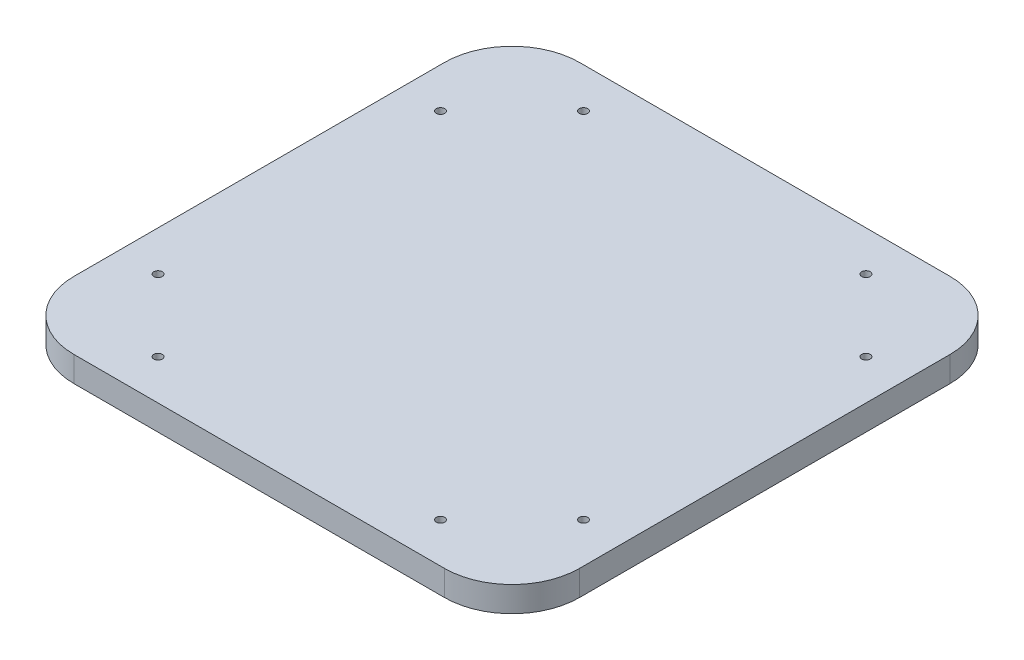
SolidWorks part; units mm, degrees
ref_plane "Front Plane" through (0, 0, 0) normal (0, 0, 1) x (1, 0, 0)
ref_plane "Top Plane" through (0, 0, 0) normal (0, 1, 0) x (1, 0, 0)
ref_plane "Right Plane" through (0, 0, 0) normal (1, 0, 0) x (0, 0, -1)
sketch "Sketch1" plane through (0, 0, 0) normal (0, 1, 0) x (1, 0, 0)
  line L1 (-150, -150) -> (150, -150)
  line L2 (-150, -150) -> (-150, 150)
  line L3 (-150, 150) -> (150, 150)
  line L4 (150, -150) -> (150, 150)
  line L5 (-150, -150) -> (150, 150) construction
  line L6 (-150, 150) -> (150, -150) construction
  point P0 (0, 0)
  dimension "D1" = 300
  dimension "D2" = 300
extrude "Boss-Extrude1" add sketch "Sketch1" along normal blind 15
sketch "Sketch2" plane through (0, 15, 0) normal (0, 1, 0) x (1, 0, 0)
  line L0 (-126.2132, 83.7868) -> (-83.7868, 126.2132) construction
  line L1 (-105, -105) -> (105, -105) construction
  line L2 (-105, -105) -> (-105, 105) construction
  line L3 (-105, 105) -> (105, 105) construction
  line L4 (105, -105) -> (105, 105) construction
  line L5 (-105, -105) -> (105, 105) construction
  line L6 (-105, 105) -> (105, -105) construction
  line L7 (-130.725, 85.9416) -> (-118.5355, 111.4645) construction
  line L8 (-111.4645, 118.5355) -> (-85.9416, 130.725) construction
  line L9 (-124.0584, 79.275) -> (-98.5355, 91.4645) construction
  line L10 (-91.4645, 98.5355) -> (-79.275, 124.0584) construction
  line L11 (83.7868, 126.2132) -> (126.2132, 83.7868) construction
  line L12 (79.275, 124.0584) -> (91.4645, 98.5355) construction
  line L13 (85.9416, 130.725) -> (111.4645, 118.5355) construction
  line L14 (118.5355, 111.4645) -> (130.725, 85.9416) construction
  line L15 (98.5355, 91.4645) -> (124.0584, 79.275) construction
  line L16 (126.2132, -83.7868) -> (83.7868, -126.2132) construction
  line L17 (124.0584, -79.275) -> (98.5355, -91.4645) construction
  line L18 (130.725, -85.9416) -> (118.5355, -111.4645) construction
  line L19 (111.4645, -118.5355) -> (85.9416, -130.725) construction
  line L20 (91.4645, -98.5355) -> (79.275, -124.0584) construction
  line L21 (-83.7868, -126.2132) -> (-126.2132, -83.7868) construction
  line L22 (-79.275, -124.0584) -> (-91.4645, -98.5355) construction
  line L23 (-85.9416, -130.725) -> (-111.4645, -118.5355) construction
  line L24 (-118.5355, -111.4645) -> (-130.725, -85.9416) construction
  line L25 (-98.5355, -91.4645) -> (-124.0584, -79.275) construction
  circle A0 centre (-105, 105) radius 5 construction
  circle A1 centre (-105, 105) radius 15 construction
  circle A2 centre (-83.7868, 126.2132) radius 5 construction
  circle A3 centre (-126.2132, 83.7868) radius 5 construction
  circle A4 centre (105, 105) radius 15 construction
  circle A5 centre (83.7868, 126.2132) radius 5 construction
  circle A6 centre (126.2132, 83.7868) radius 5 construction
  circle A7 centre (105, -105) radius 15 construction
  circle A8 centre (126.2132, -83.7868) radius 5 construction
  circle A9 centre (83.7868, -126.2132) radius 5 construction
  circle A10 centre (-105, -105) radius 15 construction
  circle A11 centre (-83.7868, -126.2132) radius 5 construction
  circle A12 centre (-126.2132, -83.7868) radius 5 construction
  point P0 (0, 0)
  point P11 (-105, 105)
  point P66 (0, 0)
  dimension "D2" = 30
  dimension "D3" = 10
  dimension "D4" = 10
  dimension "D5" = 10
  dimension "D1" = 210
  dimension "D6" = 60
  dimension "D7" = 45
  dimension "D8" = 4
sketch "Sketch3" plane through (0, 15, 0) normal (0, 1, 0) x (1, 0, 0)
  circle A0 centre (-83.7868, 126.2132) radius 2.5
  circle A1 centre (-126.2132, 83.7868) radius 2.5
  circle A2 centre (126.2132, 83.7868) radius 2.5
  circle A3 centre (83.7868, 126.2132) radius 2.5
  circle A4 centre (83.7868, -126.2132) radius 2.5
  circle A5 centre (126.2132, -83.7868) radius 2.5
  circle A6 centre (-126.2132, -83.7868) radius 2.5
  circle A7 centre (-83.7868, -126.2132) radius 2.5
  point P21 (0, 0)
  dimension "D1" = 5
  dimension "D2" = 4
extrude "Cut-Extrude1" cut sketch "Sketch3" against normal through all
fillet "Fillet1" radius 40 4 edges at (-150, 7.5, 150) (-150, 7.5, -150) (150, 7.5, 150) (150, 7.5, -150)
